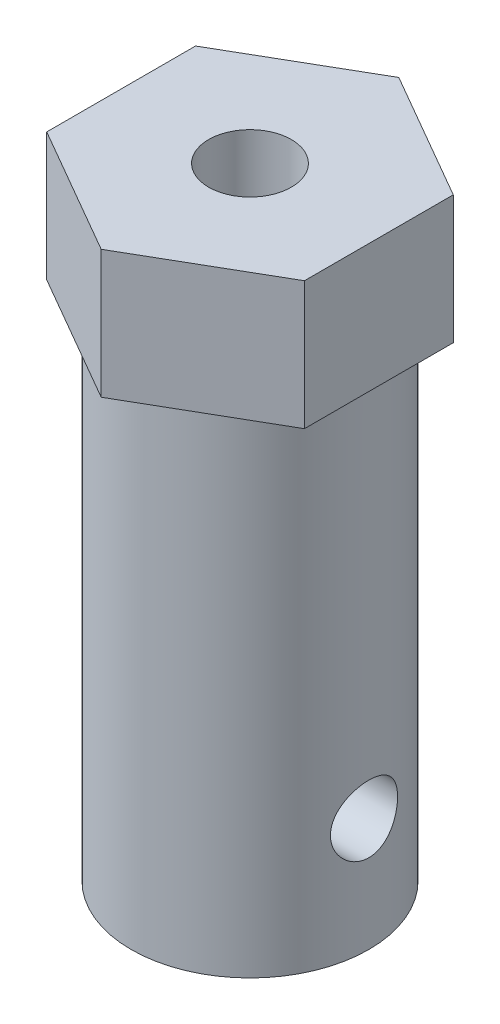
SolidWorks part; units mm, degrees
material "Brass"
ref_plane "Front" through (0, 0, 0) normal (0, 0, 1) x (1, 0, 0)
ref_plane "Top" through (0, 0, 0) normal (0, 1, 0) x (1, 0, 0)
ref_plane "Right" through (0, 0, 0) normal (1, 0, 0) x (0, 0, -1)
sketch "Sketch1" plane through (0, 0, 0) normal (0, 1, 0) x (1, 0, 0)
  circle A0 centre (0, 0) radius 5.75
  dimension "D1" = 11.5
extrude "cylinderBase" add sketch "Sketch1" along normal blind 30.07
sketch "Sketch2" plane through (0, 30.07, 0) normal (0, 1, 0) x (1, 0, 0)
  circle A2 centre (0, 0) radius 3.34
  circle A3 centre (0, 0) radius 3.34
  dimension "D1" = 2.41
extrude "throughHole" cut sketch "Sketch2" against normal through all
sketch "Sketch3" plane through (0, 30.07, 0) normal (0, 1, 0) x (1, 0, 0)
  line L1 (0, -7.2) -> (6.2354, -3.6)
  line L2 (6.2354, -3.6) -> (6.2354, 3.6)
  line L3 (6.2354, 3.6) -> (0, 7.2)
  line L4 (0, 7.2) -> (-6.2354, 3.6)
  line L5 (-6.2354, 3.6) -> (-6.2354, -3.6)
  line L6 (-6.2354, -3.6) -> (0, -7.2)
  circle A0 centre (0, 0) radius 6.2354 construction
  dimension "D1" = 7.2
extrude "Boss-Extrude2" add sketch "Sketch3" against normal blind 6.2
sketch "Sketch4" plane through (0, 30.07, 0) normal (0, 1, 0) x (1, 0, 0)
  circle A0 centre (0, 0) radius 2
  dimension "D1" = 4
extrude "Cut-Extrude2" cut sketch "Sketch4" against normal through all
sketch "Sketch5" plane through (0, 0, 0) normal (1, 0, 0) x (0, 0, -1)
  line L0 (0, 3.85) -> (0, 7.1) construction
  circle A0 centre (0, 5.475) radius 1.625
  dimension "D2" = 3.25
  dimension "D1" = 3.85
extrude "Cut-Extrude3" cut sketch "Sketch5" against normal through all both and the other way through all
